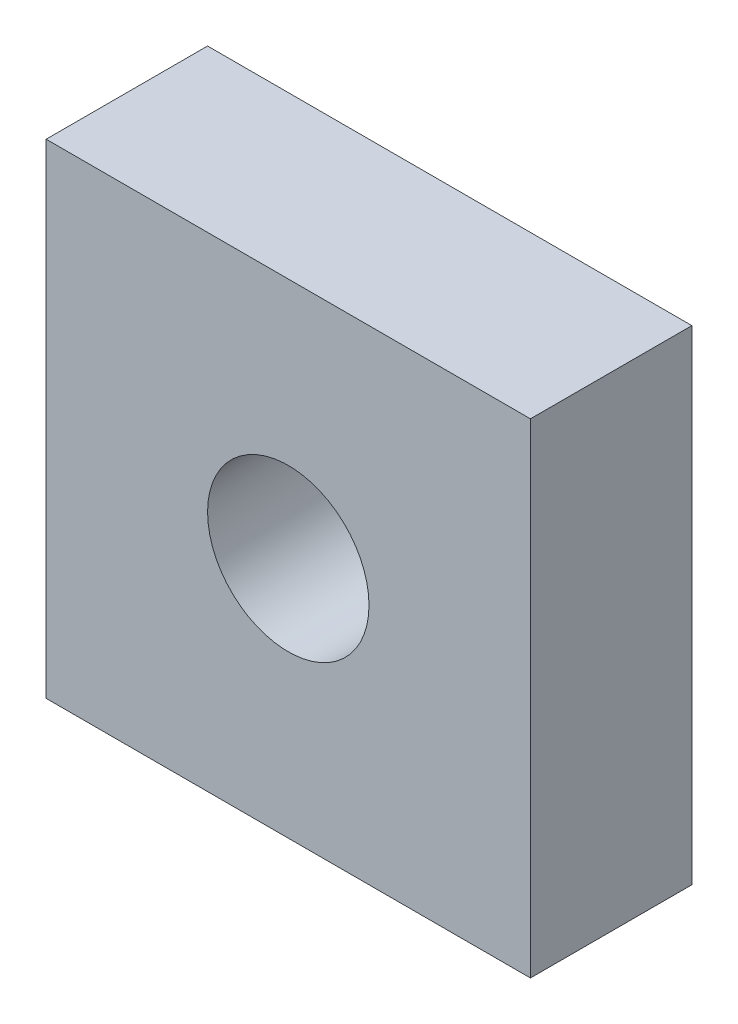
SolidWorks part; units mm, degrees
ref_plane "Front Plane" through (0, 0, 0) normal (0, 0, 1) x (1, 0, 0)
ref_plane "Top Plane" through (0, 0, 0) normal (0, 1, 0) x (1, 0, 0)
ref_plane "Right Plane" through (0, 0, 0) normal (1, 0, 0) x (0, 0, -1)
sketch "Sketch1" plane through (0, 0, 0) normal (0, 0, 1) x (1, 0, 0)
  line L0 (0, 0) -> (30, 0)
  line L1 (30, 0) -> (30, 30)
  line L2 (30, 30) -> (0, 30)
  line L3 (0, 30) -> (0, 0)
  circle A0 centre (15, 15) radius 5
  dimension "D5" = 10
  dimension "D1" = 30
  dimension "D2" = 30
  dimension "D3" = 15
  dimension "D4" = 15
extrude "Boss-Extrude1" add sketch "Sketch1" along normal blind 10
